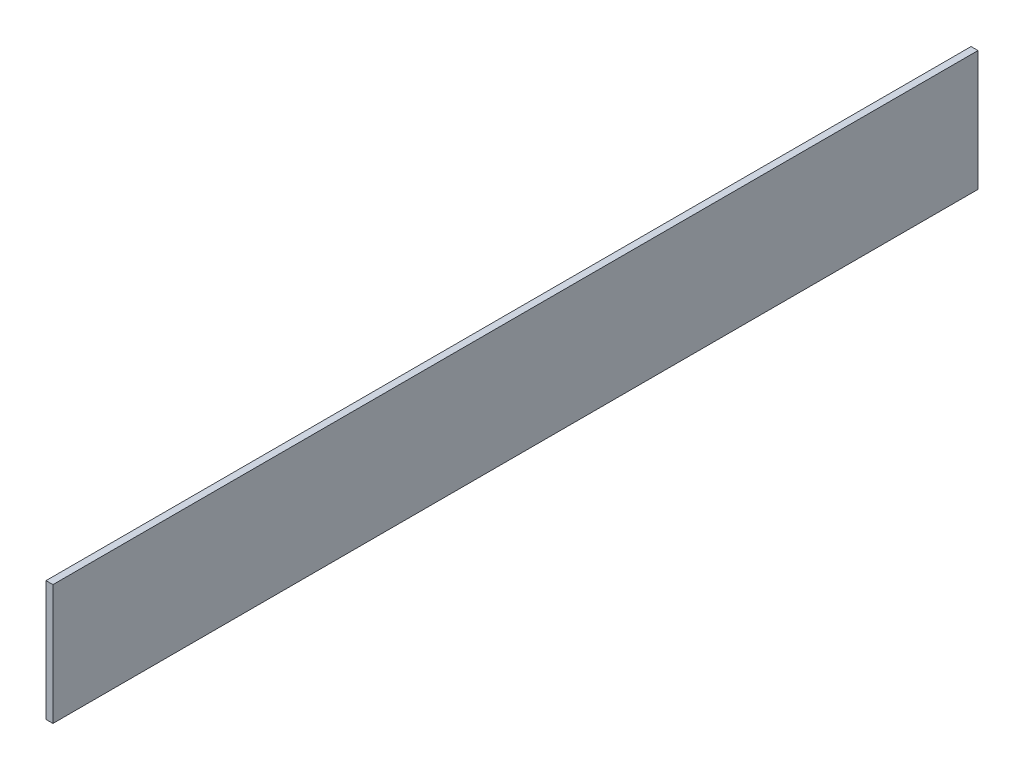
SolidWorks part; units mm, degrees
ref_plane "Front Plane" through (0, 0, 0) normal (0, 0, 1) x (1, 0, 0)
ref_plane "Top Plane" through (0, 0, 0) normal (0, 1, 0) x (1, 0, 0)
ref_plane "Right Plane" through (0, 0, 0) normal (1, 0, 0) x (0, 0, -1)
sketch "Sketch1" plane through (0, 0, 0) normal (0, 0, 1) x (1, 0, 0)
  line L1 (0, 0) -> (4.7625, 0)
  line L2 (0, 0) -> (0, 82.55)
  line L3 (0, 82.55) -> (4.7625, 82.55)
  line L4 (4.7625, 0) -> (4.7625, 82.55)
  dimension "D1" = 4.7625
  dimension "D2" = 82.55
extrude "Boss-Extrude1" add sketch "Sketch1" along normal blind 635
